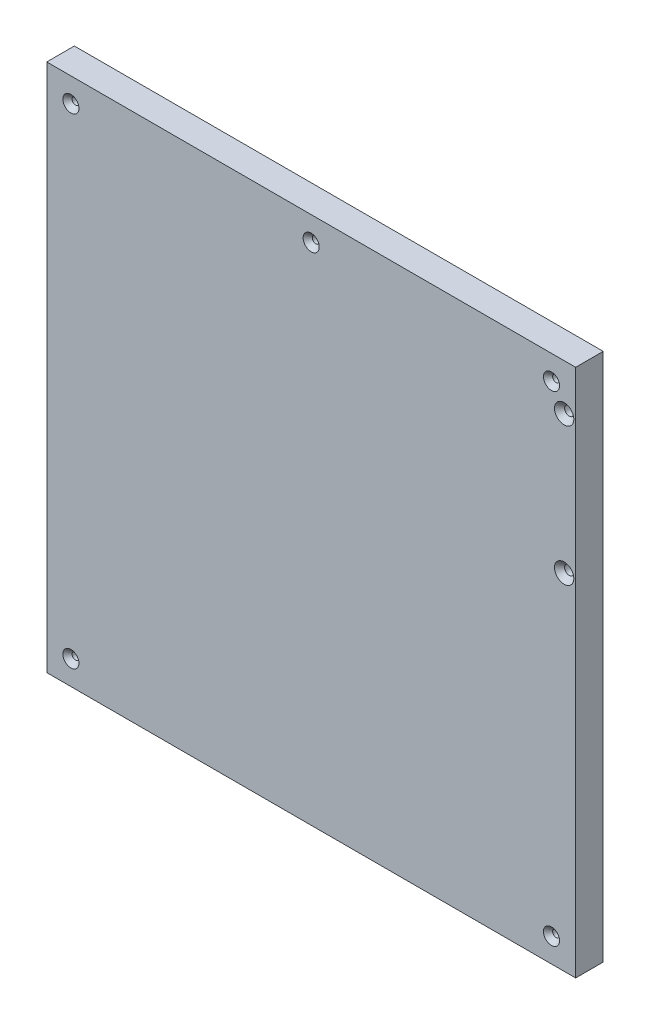
SolidWorks part; units mm, degrees
ref_plane "Спереди" through (0, 0, 0) normal (0, 0, 1) x (1, 0, 0)
ref_plane "Сверху" through (0, 0, 0) normal (0, 1, 0) x (1, 0, 0)
ref_plane "Справа" through (0, 0, 0) normal (1, 0, 0) x (0, 0, -1)
sketch "Эскиз1" plane through (0, 0, 0) normal (0, 0, 1) x (1, 0, 0)
  line L0 (115, 246.9701) -> (115, -36.9874) construction
  line L1 (0, 0) -> (230, 0)
  line L2 (0, 0) -> (0, 230)
  line L3 (0, 230) -> (230, 230)
  line L4 (230, 0) -> (230, 230)
  line L5 (-14.0533, 115) -> (258.8188, 115) construction
  line L6 (225, 242.6219) -> (225, 122.8972) construction
  circle A0 centre (219.5, 10.5) radius 1.5
  circle A1 centre (219.5, 219.5) radius 1.5
  circle A2 centre (10.5, 219.5) radius 1.5
  circle A3 centre (10.5, 10.5) radius 1.5
  circle A4 centre (115, 219.5) radius 1.5
  circle A5 centre (225, 150) radius 2
  circle A6 centre (225, 210) radius 2
  point P15 (0, 115)
  point P16 (115, 230)
  dimension "D9" = 3
  dimension "D10" = 3
  dimension "D11" = 3
  dimension "D12" = 3
  dimension "D13" = 3
  dimension "D17" = 4
  dimension "D18" = 4
  dimension "D1" = 230
  dimension "D2" = 230
  dimension "D3" = 104.5
  dimension "D4" = 104.5
  dimension "D5" = 209
  dimension "D6" = 104.5
  dimension "D7" = 104.5
  dimension "D8" = 209
  dimension "D14" = 5
  dimension "D15" = 20
  dimension "D16" = 60
extrude "Бобышка-Вытянуть1" add sketch "Эскиз1" along normal blind 12
chamfer "Фаска1" distance 2 angle 45 5 edges at (12, 10.5, 12) (221, 10.5, 12) (12, 219.5, 12) (116.5, 219.5, 12) (221, 219.5, 12)
chamfer "Фаска2" distance 2.2 angle 45 2 edges at (227, 210, 12) (227, 150, 12)
